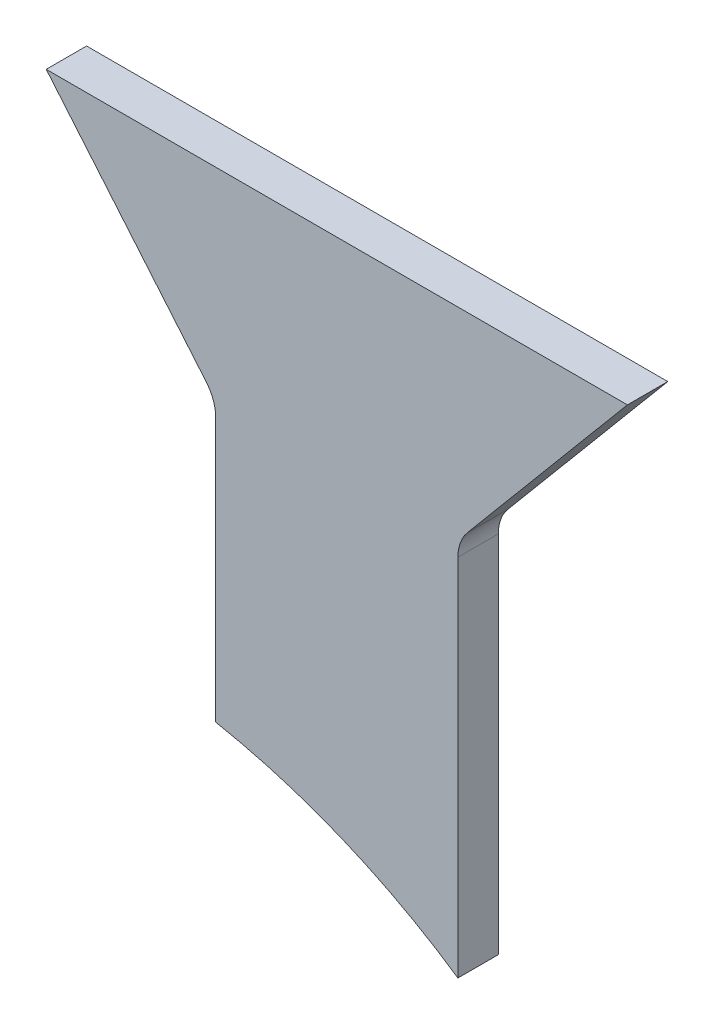
SolidWorks part; units mm, degrees
material "Plain Carbon Steel"
ref_plane "Front Plane" through (0, 0, 0) normal (0, 0, 1) x (1, 0, 0)
ref_plane "Top Plane" through (0, 0, 0) normal (0, 1, 0) x (1, 0, 0)
ref_plane "Right Plane" through (0, 0, 0) normal (1, 0, 0) x (0, 0, -1)
sketch "Sketch1" plane through (0, 0, 0) normal (0, 0, 1) x (1, 0, 0)
  line L1 (30, 0) -> (30, 93.9)
  line L2 (30, 93.9) -> (71.974, 143.9227)
  line L6 (0, 0) -> (30, 0) construction
  line L7 (0, 0) -> (0, 143.9227) construction
  line L8 (-71.974, 143.9227) -> (71.974, 143.9227)
  line L9 (-30, 24.8748) -> (-30, 93.9)
  line L10 (-30, 93.9) -> (-71.974, 143.9227)
  line L11 (0, 0) -> (0, -123.071) construction
  line L12 (-60, -132.2876) -> (44.1454, -132.2876) construction
  line L13 (-30, 0) -> (-30, 24.8748) construction
  line L14 (-30, 0) -> (0, 0) construction
  line L15 (-30, 24.8748) -> (-30, -94.1356) construction
  line L16 (30, 0) -> (30, -97.0815) construction
  arc A1 (30, 0) -> (-30, 24.8748) centre (-60, -132.2876) ccw
  circle A2 centre (-60, -132.2876) radius 160 construction
  dimension "D5" = 160
  dimension "D6" = 90
  dimension "D1" = 30
  dimension "D2" = 140
  dimension "D3" = 65.3
  dimension "D4" = 93.9
extrude "Funnel - Side Panel" add sketch "Sketch1" along normal blind 10
fillet "Fillet1" radius 10 2 edges at (-30, 93.9, 5) (30, 93.9, 5)
